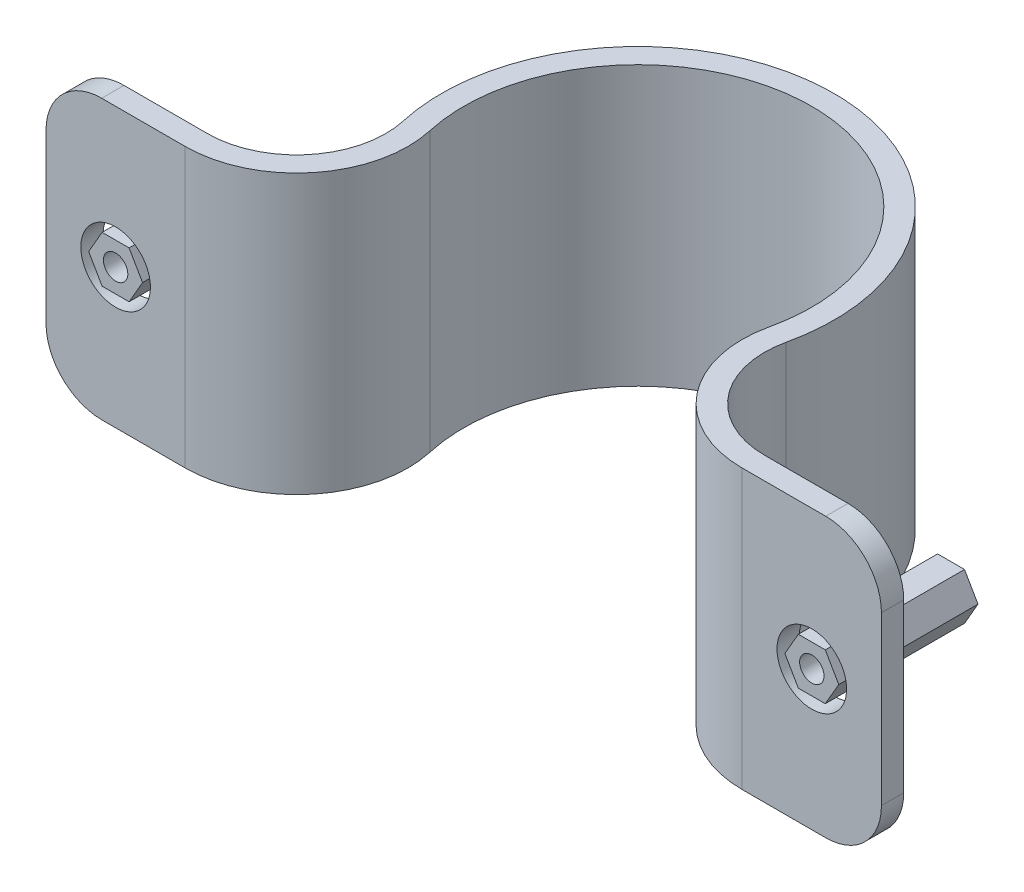
SolidWorks part; units mm, degrees
ref_plane "Front Plane" through (0, 0, 0) normal (0, 0, 1) x (1, 0, 0)
ref_plane "Top Plane" through (0, 0, 0) normal (0, 1, 0) x (1, 0, 0)
ref_plane "Right Plane" through (0, 0, 0) normal (1, 0, 0) x (0, 0, -1)
sketch "Sketch1" plane through (0, 0, 0) normal (0, 1, 0) x (1, 0, 0)
  line L0 (0, 31.75) -> (0, 33.782)
  line L1 (0, 0) -> (25.4, 0) construction
  line L2 (25.4, 0) -> (38.1, 0)
  line L3 (25.4, 2.032) -> (38.1, 2.032)
  line L4 (38.1, 2.032) -> (38.1, 0)
  line L5 (0, 33.782) -> (-4.0193, 33.782) construction
  line L6 (0, 31.75) -> (-4.0193, 31.75) construction
  line L7 (0, 31.75) -> (0, 15.875) construction
  line L8 (0, 15.875) -> (0, 0) construction
  arc A0 (15.4878, 12.3902) -> (0, 31.75) centre (0, 15.875) ccw
  arc A1 (0, 33.782) -> (17.4702, 11.9442) centre (0, 15.875) cw
  arc A4 (25.4, 2.032) -> (17.4702, 11.9442) centre (25.4, 10.16) cw
  arc A5 (25.4, 0) -> (15.4878, 12.3902) centre (25.4, 10.16) cw
  point P3 (0, 0)
  point P13 (0, 0)
  point P16 (20.6289, 14.7025)
  point P17 (20.395, 14.7025)
  dimension "D1" = 15.875
  dimension "D5" = 2.032
  dimension "D2" = 38.1
  dimension "D4" = 2.032
  dimension "D3" = 25.4
extrude "Boss-Extrude1" add sketch "Sketch1" along normal blind 25.4
mirror "Mirror2" about plane through (0, 0, 0) normal (1, 0, 0) of "Boss-Extrude1"
fillet "Fillet1" radius 5.08 4 edges at (38.1, 0, -1.016) (-38.1, 0, -1.016) (-38.1, 25.4, -1.016) (38.1, 25.4, -1.016)
sketch "Sketch2" plane through (0, 0, -2.032) normal (0, 0, -1) x (-1, 0, 0)
  line L0 (-38.1, 12.7) -> (-25.4, 12.7) construction
  line L4 (-38.1, 20.32) -> (-38.1, 5.08) construction
  line L5 (-25.4, 25.4) -> (-25.4, 0) construction
  circle A0 centre (-31.75, 12.7) radius 3.175
  point P4 (-31.75, 12.7)
  point P8 (-50.8, 12.7)
  point P9 (-58.2684, 12.7)
  dimension "D1" = 6.35
extrude "Cut-Extrude1" cut sketch "Sketch2" against normal through all
mirror "Mirror1" about plane through (0, 0, 0) normal (1, 0, 0) of "Cut-Extrude1"
sketch "Sketch4" plane through (0, 0, 0) normal (0, 0, 1) x (1, 0, 0)
  line L0 (0, 0) -> (0, 30.9514) construction
  line L1 (-29.2922, 12.7) -> (-30.5211, 14.8285)
  line L2 (-30.5211, 14.8285) -> (-32.9789, 14.8285)
  line L3 (-32.9789, 14.8285) -> (-34.2078, 12.7)
  line L4 (-34.2078, 12.7) -> (-32.9789, 10.5715)
  line L5 (-32.9789, 10.5715) -> (-30.5211, 10.5715)
  line L6 (-30.5211, 10.5715) -> (-29.2922, 12.7)
  line L7 (30.5211, 10.5715) -> (29.2922, 12.7)
  line L8 (32.9789, 10.5715) -> (30.5211, 10.5715)
  line L9 (34.2078, 12.7) -> (32.9789, 10.5715)
  line L10 (32.9789, 14.8285) -> (34.2078, 12.7)
  line L11 (30.5211, 14.8285) -> (32.9789, 14.8285)
  line L12 (29.2922, 12.7) -> (30.5211, 14.8285)
  circle A0 centre (-31.75, 12.7) radius 2.1285 construction
  circle A1 centre (-31.75, 12.7) radius 1.1125
  circle A2 centre (31.75, 12.7) radius 2.1285 construction
  circle A3 centre (31.75, 12.7) radius 1.1125
  dimension "D2" = 1.016
  dimension "D1" = 2.4578
extrude "Boss-Extrude2" add sketch "Sketch4" against normal blind 12.7 separate body
